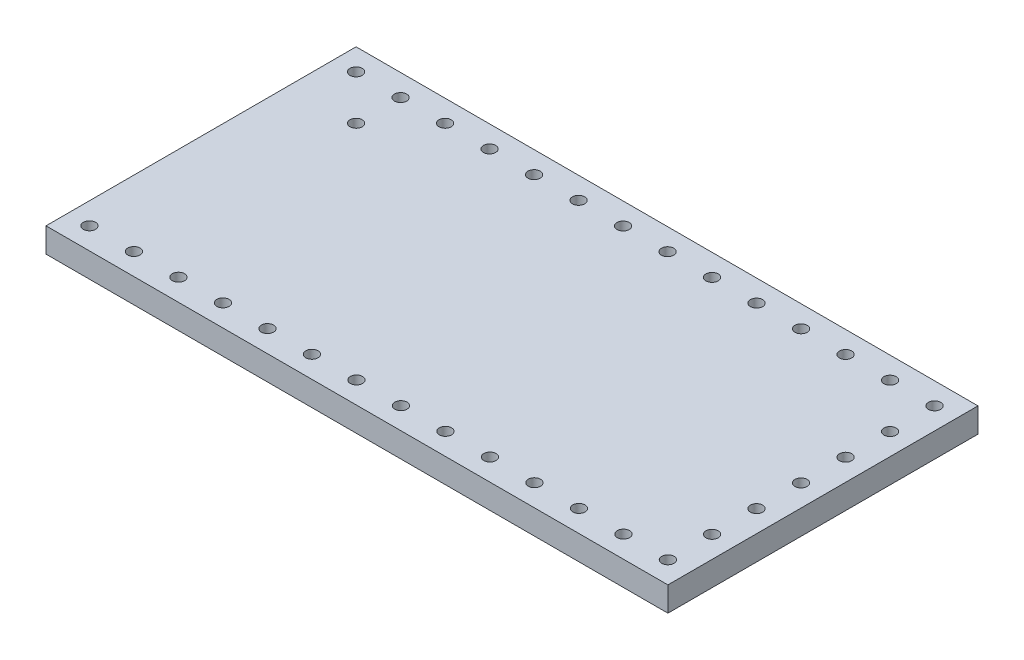
SolidWorks part; units mm, degrees
ref_plane "Front Plane" through (0, 0, 0) normal (0, 0, 1) x (1, 0, 0)
ref_plane "Top Plane" through (0, 0, 0) normal (0, 1, 0) x (1, 0, 0)
ref_plane "Right Plane" through (0, 0, 0) normal (1, 0, 0) x (0, 0, -1)
sketch "Sketch1" plane through (0, 0, 0) normal (0, 1, 0) x (1, 0, 0)
  line L0 (-55, 0) -> (55, 0) construction
  line L1 (-17.75, 8.85) -> (17.75, 8.85)
  line L2 (-17.75, 8.85) -> (-17.75, -8.85)
  line L3 (-17.75, -8.85) -> (17.75, -8.85)
  line L4 (17.75, 8.85) -> (17.75, -8.85)
  line L5 (-17.75, 8.85) -> (17.75, -8.85) construction
  line L6 (-17.75, -8.85) -> (17.75, 8.85) construction
  line L7 (16.51, 7.61) -> (16.51, -7.61) construction
  line L8 (-17.75, 7.61) -> (17.75, 7.61) construction
  line L9 (-17.75, -7.61) -> (17.75, -7.61) construction
  circle A0 centre (-16.51, 7.61) radius 0.35
  circle A1 centre (-13.97, 7.61) radius 0.35
  circle A2 centre (-11.43, 7.61) radius 0.35
  circle A3 centre (-8.89, 7.61) radius 0.35
  circle A4 centre (-6.35, 7.61) radius 0.35
  circle A5 centre (-3.81, 7.61) radius 0.35
  circle A6 centre (-1.27, 7.61) radius 0.35
  circle A7 centre (1.27, 7.61) radius 0.35
  circle A8 centre (3.81, 7.61) radius 0.35
  circle A9 centre (6.35, 7.61) radius 0.35
  circle A10 centre (8.89, 7.61) radius 0.35
  circle A11 centre (11.43, 7.61) radius 0.35
  circle A12 centre (13.97, 7.61) radius 0.35
  circle A13 centre (16.51, 7.61) radius 0.35
  circle A14 centre (16.51, -7.61) radius 0.35
  circle A15 centre (13.97, -7.61) radius 0.35
  circle A16 centre (11.43, -7.61) radius 0.35
  circle A17 centre (8.89, -7.61) radius 0.35
  circle A18 centre (6.35, -7.61) radius 0.35
  circle A19 centre (3.81, -7.61) radius 0.35
  circle A20 centre (1.27, -7.61) radius 0.35
  circle A21 centre (-1.27, -7.61) radius 0.35
  circle A22 centre (-3.81, -7.61) radius 0.35
  circle A23 centre (-6.35, -7.61) radius 0.35
  circle A24 centre (-8.89, -7.61) radius 0.35
  circle A25 centre (-11.43, -7.61) radius 0.35
  circle A26 centre (-13.97, -7.61) radius 0.35
  circle A27 centre (-16.51, -7.61) radius 0.35
  circle A28 centre (-13.97, 5.07) radius 0.35
  circle A29 centre (16.51, 5.07) radius 0.35
  circle A30 centre (16.51, 2.53) radius 0.35
  circle A31 centre (16.51, -0.01) radius 0.35
  circle A32 centre (16.51, -2.55) radius 0.35
  circle A33 centre (16.51, -5.09) radius 0.35
  point P0 (0, 0)
  dimension "D3" = 0.7
  dimension "D1" = 35.5
  dimension "D2" = 17.7
  dimension "D5" = 2.54
  dimension "D6" = 1.24
  dimension "D7" = 1.24
  dimension "D8" = 2.54
  dimension "D10" = 2.54
  dimension "D11" = 2.54
  dimension "D4" = 14
  dimension "D9" = 5
extrude "Boss-Extrude1" add sketch "Sketch1" along normal blind 1.4
